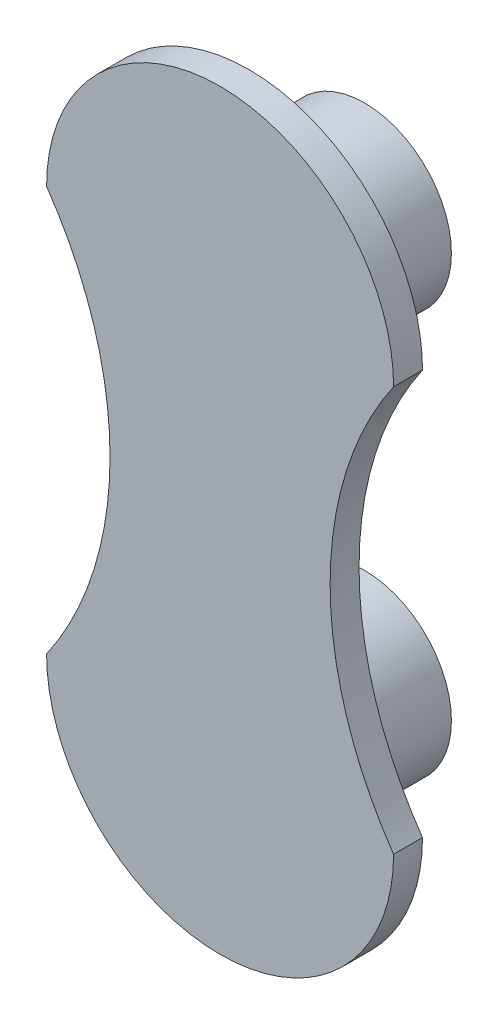
SolidWorks part; units mm, degrees
ref_plane "Front Plane" through (0, 0, 0) normal (0, 0, 1) x (1, 0, 0)
ref_plane "Top Plane" through (0, 0, 0) normal (0, 1, 0) x (1, 0, 0)
ref_plane "Right Plane" through (0, 0, 0) normal (1, 0, 0) x (0, 0, -1)
sketch "Sketch1" plane through (0, 0, 0) normal (0, 0, 1) x (1, 0, 0)
  line L0 (-1.3127, 59.1705) -> (0, 59.1705) construction
  line L1 (0, 59.1705) -> (0, -29.7295) construction
  arc A0 (38.1, 59.1705) -> (-38.1, 59.1705) centre (0, 59.1705) ccw
  arc A1 (-38.1, -29.7295) -> (38.1, -29.7295) centre (0, -29.7295) ccw
  arc A2 (38.1, 59.1705) -> (38.1, -29.7295) centre (102.0335, 14.7205) ccw
  arc A3 (-38.1, 59.1705) -> (-38.1, -29.7295) centre (-102.0335, 14.7205) cw
  dimension "D1" = 76.2
  dimension "D2" = 76.2
  dimension "D3" = 88.9
extrude "Boss-Extrude1" add sketch "Sketch1" along normal blind 6.35
sketch "Sketch2" plane through (0, 0, 0) normal (0, 0, -1) x (-1, 0, 0)
  circle A0 centre (0, 59.1705) radius 19.05
  circle A1 centre (0, -29.7295) radius 19.05
  arc A2 (-38.1, -29.7295) -> (38.1, -29.7295) centre (0, -29.7295) ccw construction
  dimension "D1" = 38.1
  dimension "D2" = 38.1
  dimension "D3" = 88.9
  dimension "D4" = 0
extrude "Boss-Extrude2" add sketch "Sketch2" along normal blind 25.4
